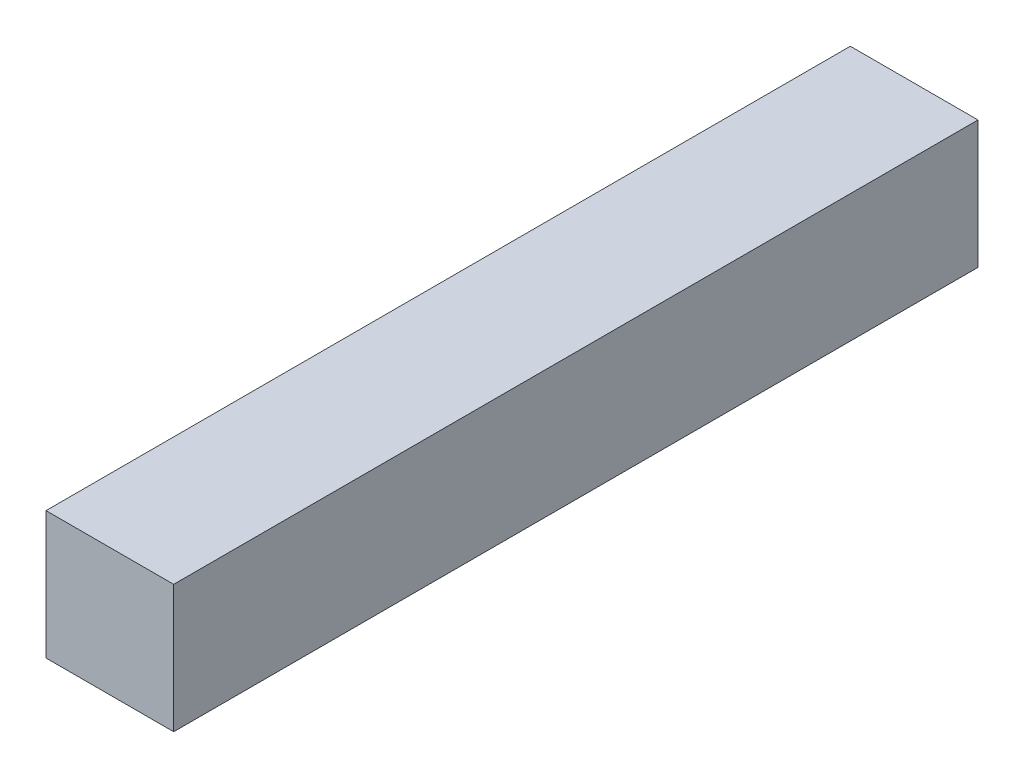
SolidWorks part; units mm, degrees
ref_plane "Front Plane" through (0, 0, 0) normal (0, 0, 1) x (1, 0, 0)
ref_plane "Top Plane" through (0, 0, 0) normal (0, 1, 0) x (1, 0, 0)
ref_plane "Right Plane" through (0, 0, 0) normal (1, 0, 0) x (0, 0, -1)
sketch "Sketch1" plane through (0, 0, 0) normal (0, 0, 1) x (1, 0, 0)
  line L1 (-1.5875, -1.5875) -> (1.5875, -1.5875)
  line L2 (-1.5875, -1.5875) -> (-1.5875, 1.5875)
  line L3 (-1.5875, 1.5875) -> (1.5875, 1.5875)
  line L4 (1.5875, -1.5875) -> (1.5875, 1.5875)
  line L5 (-1.5875, -1.5875) -> (1.5875, 1.5875) construction
  line L6 (-1.5875, 1.5875) -> (1.5875, -1.5875) construction
  point P0 (0, 0)
extrude "Boss-Extrude1" add sketch "Sketch1" along normal blind 20
